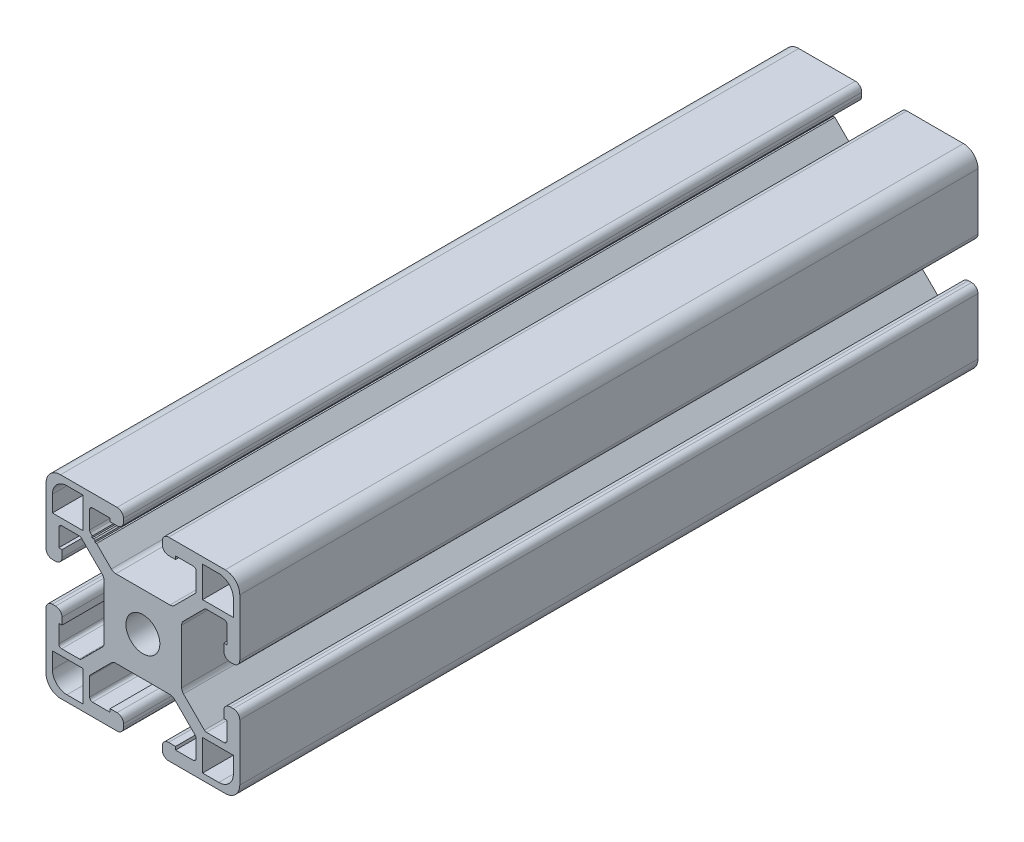
SolidWorks part; units mm, degrees
ref_plane "Front Plane" through (0, 0, 0) normal (0, 0, 1) x (1, 0, 0)
ref_plane "Top Plane" through (0, 0, 0) normal (0, 1, 0) x (1, 0, 0)
ref_plane "Right Plane" through (0, 0, 0) normal (1, 0, 0) x (0, 0, -1)
sketch "Sketch2" plane through (0, 0, 0) normal (0, 0, 1) x (1, 0, 0)
  line L0 (0, 20) -> (0, -20) construction
  line L1 (-20, 0) -> (20, 0) construction
  line L2 (4, -20) -> (20, -20)
  line L3 (20, -20) -> (20, -4)
  line L5 (6.75, -17.36) -> (10.4, -17.36)
  line L7 (0, 0) -> (20, -20) construction
  line L9 (17.36, -6.75) -> (17.36, -10.4)
  line L11 (10.4334, -8.5666) -> (8.5666, -10.4334) construction
  line L12 (11, -16.76) -> (11, -12.8668)
  line L13 (6.1332, -8) -> (11, -12.8668)
  line L14 (16.76, -11) -> (12.8668, -11)
  line L15 (8, -6.1332) -> (12.8668, -11)
  line L16 (4, -20) -> (4, -16.7)
  line L18 (4, -16.7) -> (6.75, -16.7)
  line L19 (6.75, -16.7) -> (6.75, -17.36)
  line L20 (20, -4) -> (16.7, -4)
  line L21 (16.7, -4) -> (16.7, -6.75)
  line L22 (16.7, -6.75) -> (17.36, -6.75)
  line L23 (6.75, -17.36) -> (6.75, -20) construction
  circle A0 centre (0, 0) radius 3.5
  arc A1 (10.4, -17.36) -> (11, -16.76) centre (10.4, -16.76) ccw
  arc A2 (17.36, -10.4) -> (16.76, -11) centre (16.76, -10.4) cw
  point P8 (0, -8)
  point P16 (9.5, -9.5)
  dimension "Center Hole Diameter" = 7
  dimension "D3" = 0.6
  dimension "Rail Height" = 40
  dimension "Rail Width" = 40
  dimension "T-Slot Width" = 8
  dimension "Slot Depth" = 12
  dimension "Inner Slot Width" = 22
  dimension "D1" = 2.75
  dimension "D2" = 3.3
  dimension "D4" = 0.66
sketch "Sketch3" plane through (0, 0, 0) normal (1, 0, 0) x (0, 0, -1)
  line L0 (-76.2, -20) -> (76.2, -20) construction
  line L1 (-50.8, 0) -> (50.8, 0) construction
  dimension "Length" = 152.4
  dimension "D1" = 25.4
sketch "Sketch4" plane through (0, 0, 0) normal (0, 0, 1) x (1, 0, 0)
  line L1 (20, -17) -> (20, -5.32)
  line L2 (20, -4) -> (16.7, -4) construction
  line L3 (16.7, -4) -> (16.7, -6.75) construction
  line L7 (18.02, -4) -> (18.68, -4)
  line L9 (16.7, -5.32) -> (16.7, -6.75)
  line L10 (16.7, -6.75) -> (17.36, -6.75)
  line L11 (17.36, -6.75) -> (17.36, -10.4)
  line L13 (16.76, -11) -> (13.1153, -11)
  line L18 (16.76, -11) -> (12.8668, -11) construction
  line L20 (8, -6.1332) -> (12.8668, -11) construction
  line L22 (4, -20) -> (20, -20) construction
  line L23 (20, -20) -> (20, -4) construction
  line L24 (17, -20) -> (5.32, -20)
  line L25 (4, -18.02) -> (4, -18.68)
  line L26 (4, -20) -> (4, -16.7) construction
  line L27 (4, -16.7) -> (6.75, -16.7) construction
  line L28 (5.32, -16.7) -> (6.75, -16.7)
  line L29 (6.75, -16.7) -> (6.75, -17.36)
  line L30 (6.75, -17.36) -> (10.4, -17.36)
  line L31 (6.1332, -8) -> (11, -12.8668) construction
  line L32 (11, -16.76) -> (11, -12.8668) construction
  line L33 (11, -13.1153) -> (11, -16.76)
  line L34 (0, -8) -> (5.5865, -8)
  line L35 (6.5199, -8.3866) -> (10.8243, -12.691)
  line L36 (12.691, -10.8243) -> (8.3866, -6.5199)
  line L37 (8, 0) -> (8, -5.5865)
  line L38 (-20, 0) -> (20, 0) construction
  line L39 (15.68, -18.68) -> (12.32, -18.68)
  line L40 (12.32, -18.68) -> (12.32, -12.32)
  line L41 (18.68, -12.32) -> (18.68, -15.68)
  line L42 (12.32, -12.32) -> (18.68, -12.32)
  line L43 (0, 0) -> (20, -20) construction
  line L44 (12.32, -18.68) -> (12.32, -20) construction
  line L45 (11, -14.9376) -> (12.32, -14.9376) construction
  line L46 (0, -8) -> (0, -3.5)
  line L47 (8, 0) -> (3.5, 0)
  arc A1 (18.68, -4) -> (20, -5.32) centre (18.68, -5.32) cw
  arc A10 (16.7, -5.32) -> (18.02, -4) centre (18.02, -5.32) cw
  arc A12 (17, -20) -> (20, -17) centre (17, -17) ccw
  arc A13 (4, -18.02) -> (5.32, -16.7) centre (5.32, -18.02) cw
  arc A14 (4, -18.68) -> (5.32, -20) centre (5.32, -18.68) ccw
  arc A15 (10.4, -17.36) -> (11, -16.76) centre (10.4, -16.76) ccw construction
  arc A16 (10.4, -17.36) -> (11, -16.76) centre (10.4, -16.76) ccw
  arc A17 (10.8243, -12.691) -> (11, -13.1153) centre (10.4, -13.1153) cw
  arc A18 (5.5865, -8) -> (6.5199, -8.3866) centre (5.5865, -9.32) cw
  arc A19 (16.76, -11) -> (17.36, -10.4) centre (16.76, -10.4) ccw construction
  arc A20 (16.76, -11) -> (17.36, -10.4) centre (16.76, -10.4) ccw
  arc A21 (12.691, -10.8243) -> (13.1153, -11) centre (13.1153, -10.4) ccw
  arc A22 (8, -5.5865) -> (8.3866, -6.5199) centre (9.32, -5.5865) ccw
  arc A23 (18.68, -15.68) -> (15.68, -18.68) centre (15.68, -15.68) cw
  circle A24 centre (0, 0) radius 3.5 construction
  arc A25 (0, -3.5) -> (3.5, 0) centre (0, 0) ccw
  point P74 (4, -18.35)
  dimension "D2" = 1.32
  dimension "D1" = 1.32
  dimension "D3" = 3
  dimension "D4" = 3
extrude "Boss-Extrude1" add sketch "Sketch4" along normal mid plane 152.4
mirror "Mirror1" about plane through (0, 0, 0) normal (1, 0, 0) of bodies 134
mirror "Mirror2" about plane through (0, 0, 0) normal (0, 1, 0) of bodies 135
sketch "Sketch5" plane through (0, 0, 0) normal (0, 0, 1) x (1, 0, 0)
  line L1 (-10.4532, 12.32) -> (-10.4532, 11.99)
  line L2 (-6.5199, 8.3866) -> (-10.8243, 12.691) construction
  line L3 (-10.4532, 11.99) -> (-10.1232, 11.99)
  line L4 (-10.1232, 11.99) -> (-9.8899, 11.7567)
  line L5 (-9.8899, 11.7567) -> (-9.8899, 11.4267)
  line L6 (-9.8899, 11.4267) -> (-9.5599, 11.4267)
  line L7 (-10.4532, 12.32) -> (-9.5599, 12.32)
  line L8 (-9.5599, 12.32) -> (-9.5599, 11.4267)
  dimension "D1" = 0.33
extrude "Cut-Extrude1" cut sketch "Sketch5" against normal through all both and the other way through all
equation "\"D3@Sketch2\"=\"T-Slot Width@Sketch2\"*0.075"
equation "\"D1@Boss-Extrude1\"=\"Length@Sketch3\""
equation "\"D1@Sketch2\"=\"Inner Slot Width@Sketch2\"*0.125"
equation "\"D2@Sketch2\"=\"Slot Depth@Sketch2\"*0.275"
equation "\"D4@Sketch2\"=\"D2@Sketch2\"*0.2"
equation "\"D1@Sketch4\"=\"D2@Sketch2\"*0.4"
equation "\"D2@Sketch4\"=\"D1@Sketch4\""
equation "\"D3@Sketch4\"=\"Rail Height@Sketch2\"*0.075"
equation "\"D4@Sketch4\"=\"Rail Height@Sketch2\"*0.075"
equation "\"D1@Sketch5\"=\"D4@Sketch2\"*0.5"
